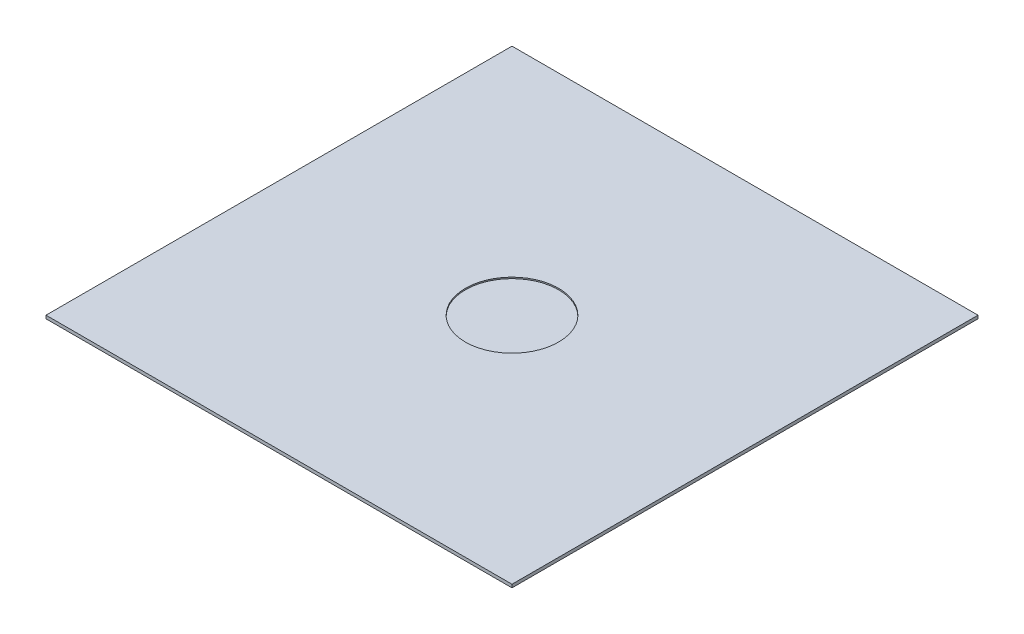
SolidWorks part; units mm, degrees
material "Glass"
ref_plane "Front Plane" through (0, 0, 0) normal (0, 0, 1) x (1, 0, 0)
ref_plane "Top Plane" through (0, 0, 0) normal (0, 1, 0) x (1, 0, 0)
ref_plane "Right Plane" through (0, 0, 0) normal (1, 0, 0) x (0, 0, -1)
sketch "Sketch1" plane through (0, 0, 0) normal (0, 1, 0) x (1, 0, 0)
  line L1 (-12.5, -12.5) -> (12.5, -12.5)
  line L2 (-12.5, -12.5) -> (-12.5, 12.5)
  line L3 (-12.5, 12.5) -> (12.5, 12.5)
  line L4 (12.5, -12.5) -> (12.5, 12.5)
  line L5 (-12.5, -12.5) -> (12.5, 12.5) construction
  line L6 (-12.5, 12.5) -> (12.5, -12.5) construction
  point P0 (0, 0)
  dimension "D1" = 25
extrude "Boss-Extrude1" add sketch "Sketch1" along normal blind 0.17
sketch "Sketch2" plane through (0, 0.17, 0) normal (0, 1, 0) x (1, 0, 0)
  circle A0 centre (0, 0) radius 2.5
  dimension "D1" = 5
extrude "Cut-Extrude1" cut sketch "Sketch2" against normal blind 0.07
